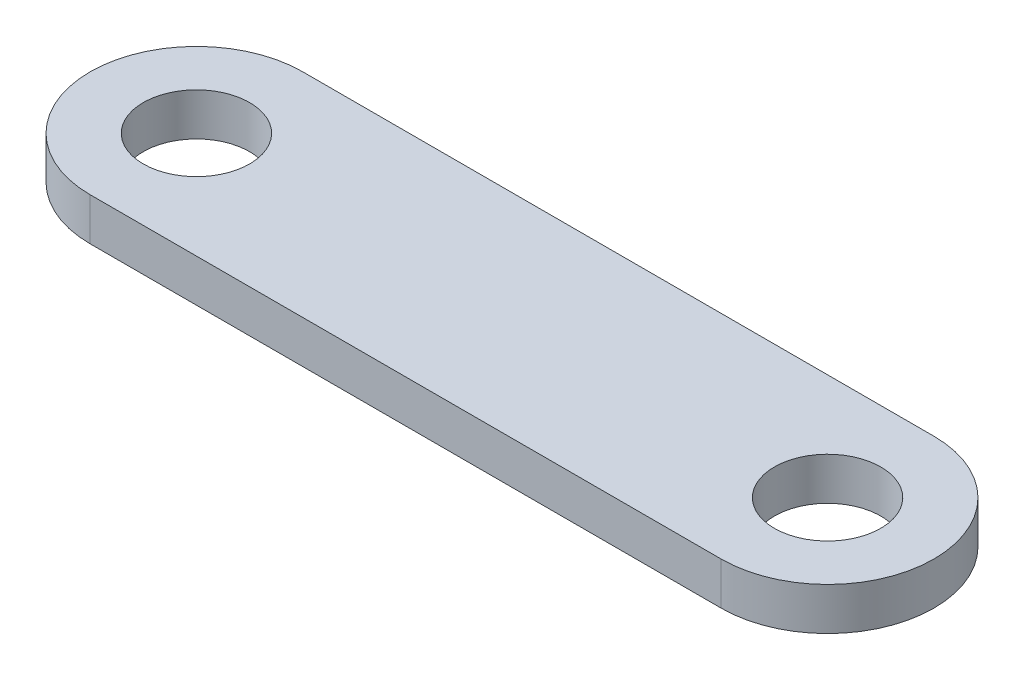
SolidWorks part; units mm, degrees
ref_plane "Front Plane" through (0, 0, 0) normal (0, 0, 1) x (1, 0, 0)
ref_plane "Top Plane" through (0, 0, 0) normal (0, 1, 0) x (1, 0, 0)
ref_plane "Right Plane" through (0, 0, 0) normal (1, 0, 0) x (0, 0, -1)
sketch "Sketch1" plane through (0, 0, 0) normal (0, 1, 0) x (1, 0, 0)
  line L0 (-18.8377, 0) -> (18.8377, 0) construction
  line L1 (-18.8377, 0) -> (18.8377, 0) construction
  line L2 (-18.8377, 6.35) -> (18.8377, 6.35)
  line L3 (-18.8377, -6.35) -> (18.8377, -6.35)
  arc A0 (-18.8377, 6.35) -> (-18.8377, -6.35) centre (-18.8377, 0) ccw
  arc A1 (18.8377, -6.35) -> (18.8377, 6.35) centre (18.8377, 0) ccw
  circle A2 centre (-18.8377, 0) radius 3.175
  circle A3 centre (18.8377, 0) radius 3.175
  point P3 (0, 0)
  dimension "D2" = 6.35
  dimension "D3" = 6.35
  dimension "D4" = 6.35
  dimension "D1" = 37.6753
extrude "Boss-Extrude1" add sketch "Sketch1" along normal blind 2.54
